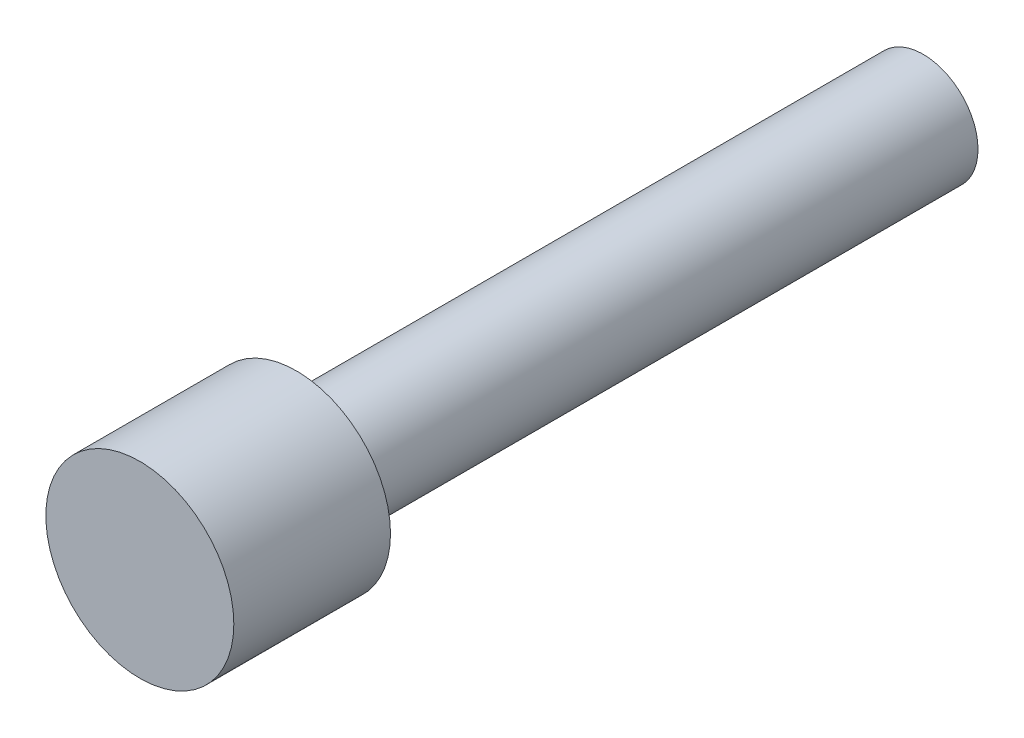
SolidWorks part; units mm, degrees
ref_plane "Front Plane" through (0, 0, 0) normal (0, 0, 1) x (1, 0, 0)
ref_plane "Top Plane" through (0, 0, 0) normal (0, 1, 0) x (1, 0, 0)
ref_plane "Right Plane" through (0, 0, 0) normal (1, 0, 0) x (0, 0, -1)
sketch "Sketch1" plane through (0, 0, 0) normal (0, 0, 1) x (1, 0, 0)
  circle A0 centre (117.2126, 333.9822) radius 1.75
  dimension "D1" = 3.5
extrude "Boss-Extrude1" add sketch "Sketch1" along normal blind 20
sketch "Sketch2" plane through (0, 0, 20) normal (0, 0, 1) x (1, 0, 0)
  circle A2 centre (117.2126, 333.9822) radius 3
  dimension "D1" = 6
extrude "Boss-Extrude2" add sketch "Sketch2" along normal blind 5
